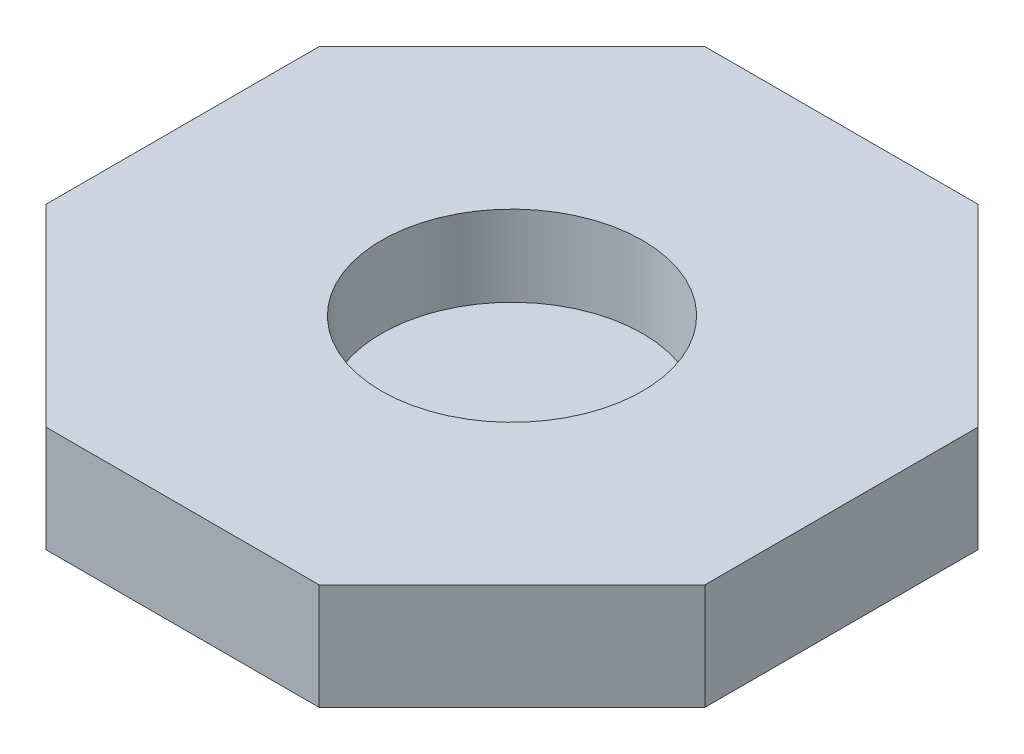
SolidWorks part; units mm, degrees
ref_plane "정면" through (0, 0, 0) normal (0, 0, 1) x (1, 0, 0)
ref_plane "윗면" through (0, 0, 0) normal (0, 1, 0) x (1, 0, 0)
ref_plane "우측면" through (0, 0, 0) normal (1, 0, 0) x (0, 0, -1)
sketch "스케치1" plane through (0, 0, 0) normal (0, 1, 0) x (1, 0, 0)
  line L0 (-55, 0) -> (55, 0) construction
  line L1 (-5.9316, 14.3201) -> (-14.3201, 5.9316)
  line L2 (-14.3201, 5.9316) -> (-14.3201, -5.9316)
  line L3 (-14.3201, -5.9316) -> (-5.9316, -14.3201)
  line L4 (-5.9316, -14.3201) -> (5.9316, -14.3201)
  line L5 (5.9316, -14.3201) -> (14.3201, -5.9316)
  line L6 (14.3201, -5.9316) -> (14.3201, 5.9316)
  line L7 (14.3201, 5.9316) -> (5.9316, 14.3201)
  line L8 (5.9316, 14.3201) -> (-5.9316, 14.3201)
  line L9 (-6.4286, 15.5201) -> (-15.5201, 6.4286)
  line L10 (-15.5201, 6.4286) -> (-15.5201, -6.4286)
  line L11 (-15.5201, -6.4286) -> (-6.4286, -15.5201)
  line L12 (-6.4286, -15.5201) -> (6.4286, -15.5201)
  line L13 (6.4286, -15.5201) -> (15.5201, -6.4286)
  line L14 (15.5201, -6.4286) -> (15.5201, 6.4286)
  line L15 (15.5201, 6.4286) -> (6.4286, 15.5201)
  line L16 (6.4286, 15.5201) -> (-6.4286, 15.5201)
  circle A0 centre (0, 0) radius 15.5 construction
  dimension "D1" = 31
  dimension "D2" = 1.2
extrude "보스-돌출1" add sketch "스케치1" along normal blind 5 contours L7 L8 L1 L2 L3 L4 L5 L6 | L15 L16 L9 L10 L11 L12 L13 L14 L8 L7 L6 L5 L4 L3 L2 L1
sketch "스케치3" plane through (0, 0, 0) normal (0, -1, 0) x (1, 0, 0)
  line L8 (5.4345, -13.1201) -> (13.1201, -5.4345)
  line L9 (13.1201, -5.4345) -> (13.1201, 5.4345)
  line L10 (13.1201, 5.4345) -> (5.4345, 13.1201)
  line L11 (5.4345, 13.1201) -> (-5.4345, 13.1201)
  line L12 (-5.4345, 13.1201) -> (-13.1201, 5.4345)
  line L13 (-13.1201, 5.4345) -> (-13.1201, -5.4345)
  line L14 (-13.1201, -5.4345) -> (-5.4345, -13.1201)
  line L15 (-5.4345, -13.1201) -> (5.4345, -13.1201)
  line L16 (5.9316, -14.3201) -> (14.3201, -5.9316)
  line L17 (14.3201, -5.9316) -> (14.3201, 5.9316)
  line L18 (14.3201, 5.9316) -> (5.9316, 14.3201)
  line L19 (5.9316, 14.3201) -> (-5.9316, 14.3201)
  line L20 (-5.9316, 14.3201) -> (-14.3201, 5.9316)
  line L21 (-14.3201, 5.9316) -> (-14.3201, -5.9316)
  line L22 (-14.3201, -5.9316) -> (-5.9316, -14.3201)
  line L23 (-5.9316, -14.3201) -> (5.9316, -14.3201)
  line L24 (5.9316, -14.3201) -> (14.3201, -5.9316)
  line L25 (14.3201, -5.9316) -> (14.3201, 5.9316)
  line L26 (14.3201, 5.9316) -> (5.9316, 14.3201)
  line L27 (5.9316, 14.3201) -> (-5.9316, 14.3201)
  line L28 (-5.9316, 14.3201) -> (-14.3201, 5.9316)
  line L29 (-14.3201, 5.9316) -> (-14.3201, -5.9316)
  line L30 (-14.3201, -5.9316) -> (-5.9316, -14.3201)
  line L31 (-5.9316, -14.3201) -> (5.9316, -14.3201)
  dimension "D1" = 1.2
  dimension "D2" = 1.2
extrude "컷-돌출1" cut sketch "스케치3" against normal blind 1
sketch "스케치6" plane through (0, 5, 0) normal (0, 1, 0) x (1, 0, 0)
  circle A0 centre (0, 0) radius 6.15
  dimension "D1" = 12.3
extrude "컷-돌출2" cut sketch "스케치6" against normal blind 3.8
sketch "스케치8" plane through (0, 0, 0) normal (0, -1, 0) x (1, 0, 0)
  line L8 (-5.4345, -13.1201) -> (5.4345, -13.1201)
  line L9 (5.4345, -13.1201) -> (13.1201, -5.4345)
  line L10 (13.1201, -5.4345) -> (13.1201, 5.4345)
  line L11 (13.1201, 5.4345) -> (5.4345, 13.1201)
  line L12 (5.4345, 13.1201) -> (-5.4345, 13.1201)
  line L13 (-5.4345, 13.1201) -> (-13.1201, 5.4345)
  line L14 (-13.1201, 5.4345) -> (-13.1201, -5.4345)
  line L15 (-13.1201, -5.4345) -> (-5.4345, -13.1201)
  line L16 (-5.4345, -13.1201) -> (5.4345, -13.1201)
  line L17 (5.4345, -13.1201) -> (13.1201, -5.4345)
  line L18 (13.1201, -5.4345) -> (13.1201, 5.4345)
  line L19 (13.1201, 5.4345) -> (5.4345, 13.1201)
  line L20 (5.4345, 13.1201) -> (-5.4345, 13.1201)
  line L21 (-5.4345, 13.1201) -> (-13.1201, 5.4345)
  line L22 (-13.1201, 5.4345) -> (-13.1201, -5.4345)
  line L23 (-13.1201, -5.4345) -> (-5.4345, -13.1201)
  circle A0 centre (0, 0) radius 3.15
  circle A1 centre (0, 0) radius 4.15
  dimension "D2" = 6.3
  dimension "D1" = 0
  dimension "D3" = 1
extrude "보스-돌출4" add sketch "스케치8" along normal blind 7 contours A1 A0
sketch "스케치9" plane through (0, 0, 0) normal (0, -1, 0) x (1, 0, 0)
  circle A0 centre (0, 0) radius 5
  circle A1 centre (0, 0) radius 4.15 construction
  circle A2 centre (0, 0) radius 4.15
  dimension "D1" = 10
extrude "보스-돌출5" add sketch "스케치9" along normal blind 2
